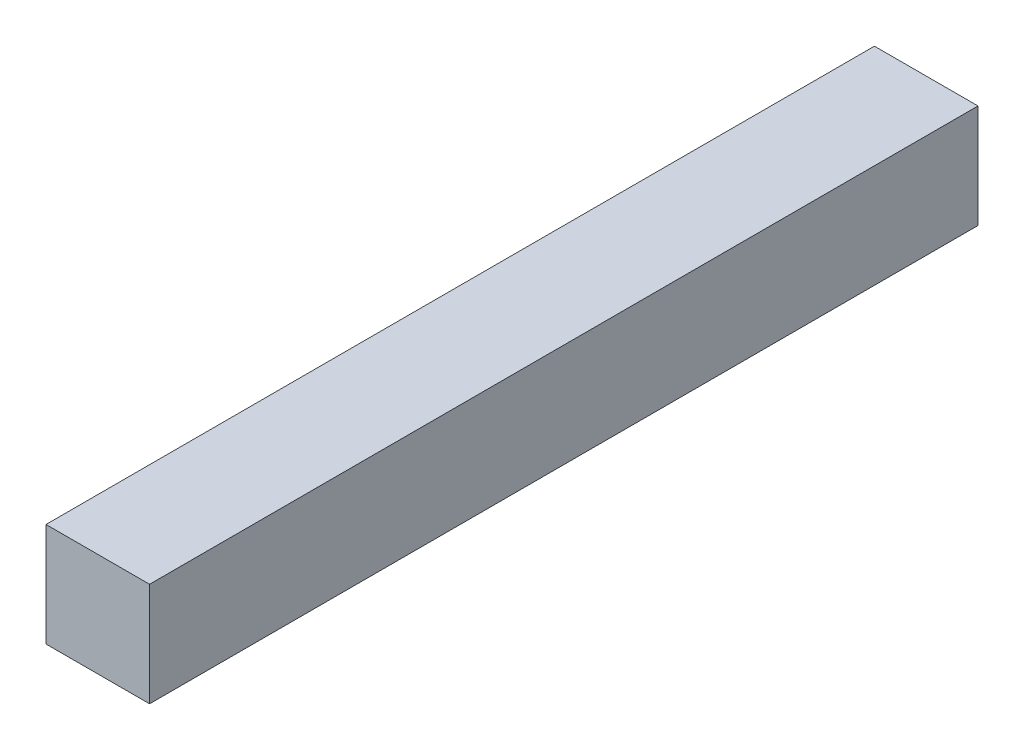
SolidWorks part; units mm, degrees
material "Stainless Steel (ferritic)"
ref_plane "Front Plane" through (0, 0, 0) normal (0, 0, 1) x (1, 0, 0)
ref_plane "Top Plane" through (0, 0, 0) normal (0, 1, 0) x (1, 0, 0)
ref_plane "Right Plane" through (0, 0, 0) normal (1, 0, 0) x (0, 0, -1)
sketch "Sketch1" plane through (0, 0, 0) normal (0, 0, 1) x (1, 0, 0)
  line L1 (-5, -5) -> (5, -5)
  line L2 (-5, -5) -> (-5, 5)
  line L3 (-5, 5) -> (5, 5)
  line L4 (5, -5) -> (5, 5)
  line L5 (-5, -5) -> (5, 5) construction
  line L6 (-5, 5) -> (5, -5) construction
  point P0 (0, 0)
extrude "Boss-Extrude1" add sketch "Sketch1" along normal blind 80
